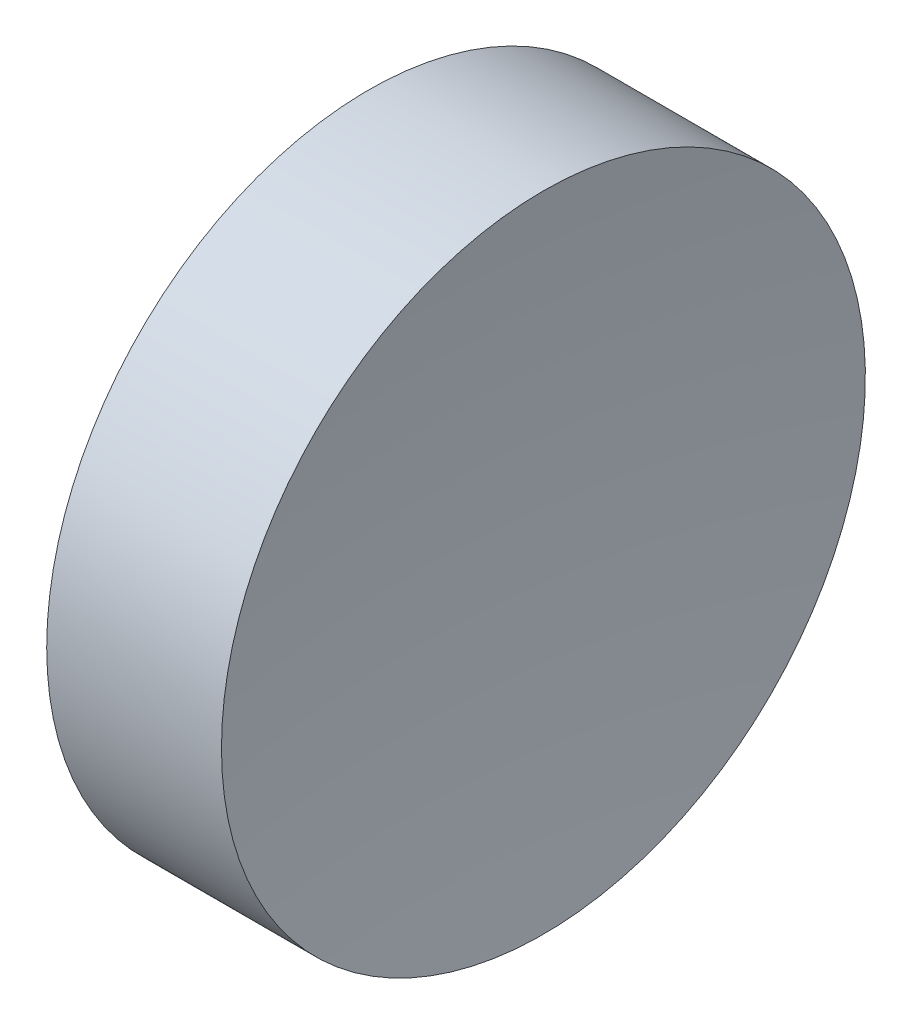
SolidWorks part; units mm, degrees
ref_plane "前视基准面" through (0, 0, 0) normal (0, 0, 1) x (1, 0, 0)
ref_plane "上视基准面" through (0, 0, 0) normal (0, 1, 0) x (1, 0, 0)
ref_plane "右视基准面" through (0, 0, 0) normal (1, 0, 0) x (0, 0, -1)
sketch "草图1" plane through (0, 0, 0) normal (0, 0, 1) x (1, 0, 0)
  line L0 (21.2249, 13.0445) -> (26.692, 13.0445) construction
  line L1 (22.1722, 13.0445) -> (22.1722, 16.1945)
  line L2 (23.6722, 13.0445) -> (22.1722, 13.0445)
  line L3 (22.1722, 16.1945) -> (23.8822, 16.1945)
  arc A0 (23.8822, 16.1945) -> (23.6722, 13.0445) centre (47.405, 13.0445) ccw
revolve "旋转1" add sketch "草图1" angle 360 about L0
